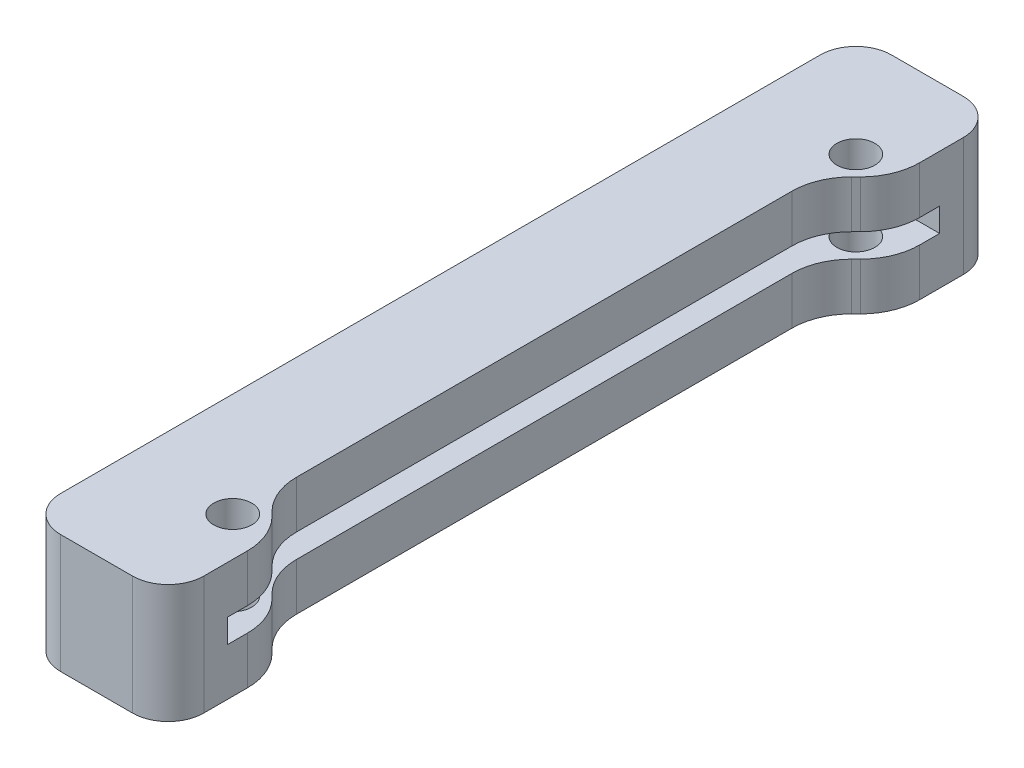
SolidWorks part; units mm, degrees
ref_plane "Front Plane" through (0, 0, 0) normal (0, 0, 1) x (1, 0, 0)
ref_plane "Top Plane" through (0, 0, 0) normal (0, 1, 0) x (1, 0, 0)
ref_plane "Right Plane" through (0, 0, 0) normal (1, 0, 0) x (0, 0, -1)
sketch "Sketch2" plane through (0, 0, 0) normal (0, 1, 0) x (1, 0, 0)
  line L0 (-85, 26.25) -> (85, 26.25) construction
  line L1 (-88.75, 30) -> (88.75, 30)
  line L2 (-88.75, 30) -> (-88.75, -30)
  line L3 (-88.75, -30) -> (88.75, -30)
  line L4 (88.75, 30) -> (88.75, -30)
  line L5 (85, 26.25) -> (85, -26.25) construction
  line L6 (-85, -26.25) -> (85, -26.25) construction
  line L7 (-85, 26.25) -> (-85, -26.25) construction
  circle A0 centre (-85, 26.25) radius 1.6
  circle A1 centre (85, 26.25) radius 1.6
  circle A2 centre (85, -26.25) radius 1.6
  circle A3 centre (-85, -26.25) radius 1.6
  point P4 (0, 30)
  point P6 (-88.75, 0)
  dimension "D4" = 3.2
  dimension "D1" = 177.5
  dimension "D2" = 60
  dimension "D3" = 3.75
sketch "Sketch3" plane through (0, 0, 0) normal (0, 1, 0) x (1, 0, 0)
  line L2 (-88.75, 30) -> (88.75, 30) construction
  line L3 (-81.6926, 30) -> (-81.6926, 26.25)
  line L4 (-88.75, -30) -> (88.75, -30) construction
  line L7 (-85, 26.25) -> (-85, -26.25) construction
  line L8 (-88.75, 30) -> (-88.75, -30) construction
  line L9 (-85, 26.25) -> (85, 26.25) construction
  line L10 (-81.6926, 26.25) -> (-85, 22.9426)
  line L11 (-81.6926, 30) -> (-81.6926, 35)
  line L12 (-81.6926, 35) -> (-93.75, 35)
  line L13 (-93.75, 35) -> (-93.75, -35)
  line L14 (-93.75, -35) -> (-81.6926, -35)
  line L15 (-81.6926, -35) -> (-81.6926, -30)
  line L16 (-93.75, 0) -> (-71.4687, 0) construction
  line L17 (-81.6926, -26.25) -> (-85, -22.9426)
  line L18 (-85, 22.9426) -> (-85, -22.9426)
  line L19 (-81.6926, -26.25) -> (-81.6926, -30)
  circle A0 centre (-85, 26.25) radius 1.6
  circle A1 centre (-85, -26.25) radius 1.6
  dimension "D1" = 45
  dimension "D2" = 5
  dimension "D3" = 5
extrude "Boss-Extrude1" add sketch "Sketch3" along normal mid plane 10
sketch "Sketch4" plane through (0, 0, 0) normal (0, 1, 0) x (1, 0, 0)
  line L0 (-88.75, -30) -> (88.75, -30) construction
  line L1 (-88.75, 30) -> (-75.5674, 30)
  line L2 (-88.75, 30) -> (-88.75, -30)
  line L3 (-88.75, -30) -> (-75.5674, -30)
  line L4 (-75.5674, 30) -> (-75.5674, -30)
extrude "Cut-Extrude1" cut sketch "Sketch4" against normal mid plane 2
fillet "Fillet1" radius 5 8 edges at (-81.6926, -3, 26.25) (-81.6926, 3, 26.25) (-85, 3, 22.9426) (-85, -3, 22.9426) (-85, -3, -22.9426) (-85, 3, -22.9426) (-81.6926, -3, -26.25) (-81.6926, 3, -26.25)
fillet "Fillet2" radius 3 4 edges at (-81.6926, 0, -35) (-93.75, 0, -35) (-93.75, 0, 35) (-81.6926, 0, 35)
